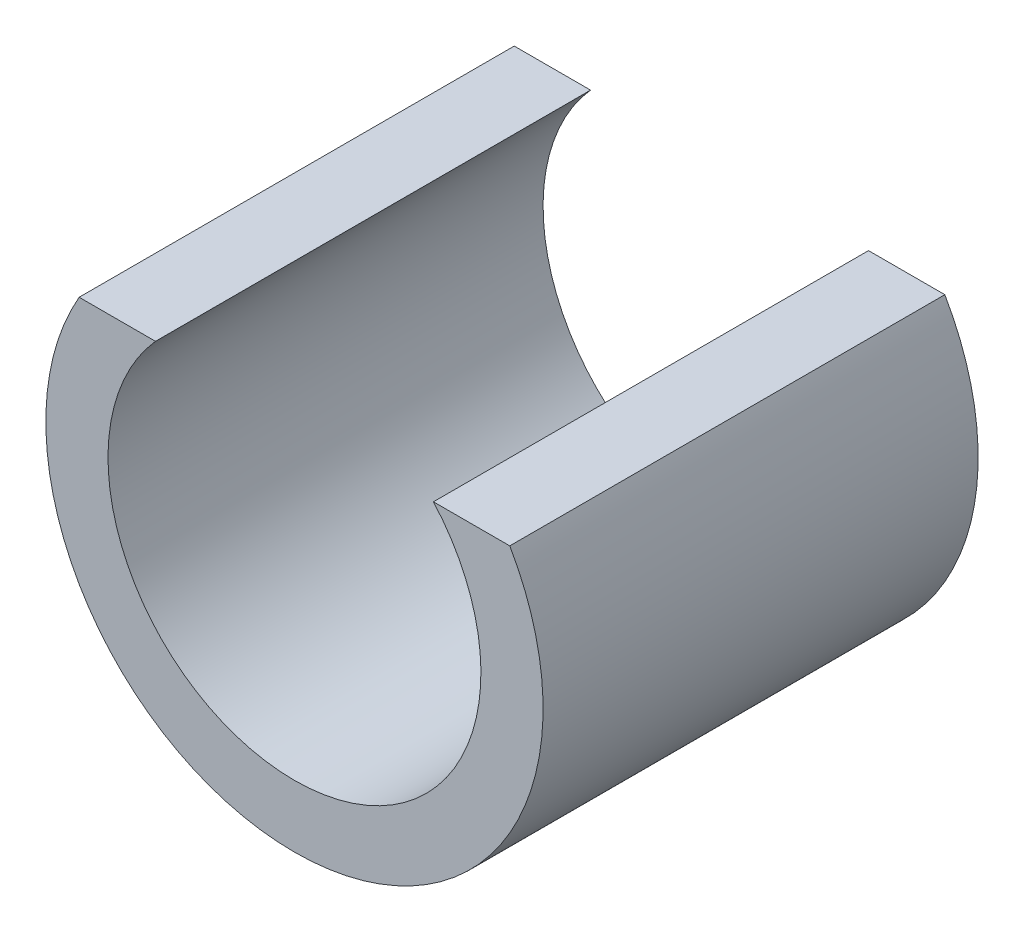
SolidWorks part; units mm, degrees
ref_plane "前视基准面" through (0, 0, 0) normal (0, 0, 1) x (1, 0, 0)
ref_plane "上视基准面" through (0, 0, 0) normal (0, 1, 0) x (1, 0, 0)
ref_plane "右视基准面" through (0, 0, 0) normal (1, 0, 0) x (0, 0, -1)
sketch "草图1" plane through (0, 0, 0) normal (0, 0, 1) x (1, 0, 0)
  line L0 (0, 0) -> (0, 1)
  line L1 (-1.7321, 1) -> (1.7321, 1)
  circle A0 centre (0, 0) radius 1.5
  circle A1 centre (0, 0) radius 2
  dimension "D1" = 1
  dimension "D2" = 4
  dimension "D3" = 3
extrude "凸台-拉伸1" add sketch "草图1" along normal blind 3.5 contours L1 A1 A0
